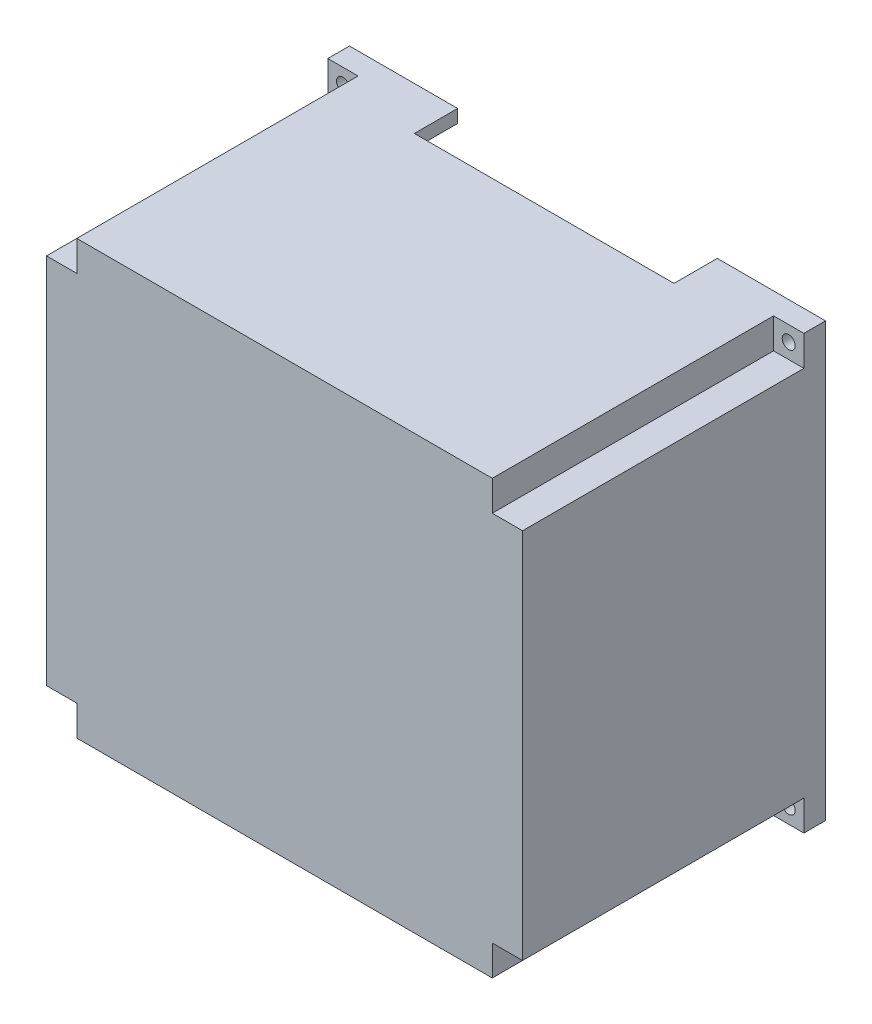
SolidWorks part; units mm, degrees
ref_plane "Front Plane" through (0, 0, 0) normal (0, 0, 1) x (1, 0, 0)
ref_plane "Top Plane" through (0, 0, 0) normal (0, 1, 0) x (1, 0, 0)
ref_plane "Right Plane" through (0, 0, 0) normal (1, 0, 0) x (0, 0, -1)
sketch "Sketch1" plane through (0, 0, 0) normal (0, 1, 0) x (1, 0, 0)
  line L1 (0, 0) -> (2794, 0)
  line L2 (0, 0) -> (0, 1778)
  line L3 (0, 1778) -> (2794, 1778)
  line L4 (2794, 0) -> (2794, 1778)
  dimension "D1" = 1778
  dimension "D2" = 2794
extrude "Boss-Extrude1" add sketch "Sketch1" along normal blind 2540
sketch "Sketch2" plane through (0, 0, -1778) normal (0, 0, -1) x (-1, 0, 0)
  line L0 (-2794, 2540) -> (0, 2540) construction
  line L1 (-2717.8, 2463.8) -> (-76.2, 2463.8)
  line L2 (-2717.8, 2463.8) -> (-2717.8, 76.2)
  line L3 (-2717.8, 76.2) -> (-76.2, 76.2)
  line L4 (-76.2, 2463.8) -> (-76.2, 76.2)
  line L5 (-2717.8, 2463.8) -> (-76.2, 76.2) construction
  line L6 (-2717.8, 76.2) -> (-76.2, 2463.8) construction
  line L7 (-2794, 2540) -> (-2794, 0) construction
  line L8 (-2794, 0) -> (0, 0) construction
  line L9 (0, 2540) -> (0, 0) construction
  point P0 (-1397, 1270)
  dimension "D1" = 76.2
  dimension "D2" = 76.2
  dimension "D3" = 76.2
  dimension "D4" = 76.2
extrude "Cut-Extrude1" cut sketch "Sketch2" against normal blind 1701.8
sketch "Sketch3" plane through (0, 0, -76.2) normal (0, 0, -1) x (-1, 0, 0)
  line L1 (-2717.8, 2463.8) -> (-2540, 2463.8)
  line L2 (-2717.8, 2463.8) -> (-2717.8, 2286)
  line L3 (-2717.8, 2286) -> (-2540, 2286)
  line L4 (-2540, 2463.8) -> (-2540, 2286)
  line L5 (-76.2, 2463.8) -> (-254, 2463.8)
  line L6 (-76.2, 2463.8) -> (-76.2, 2286)
  line L7 (-76.2, 2286) -> (-254, 2286)
  line L8 (-254, 2463.8) -> (-254, 2286)
  line L9 (-2717.8, 76.2) -> (-2540, 76.2)
  line L10 (-2717.8, 76.2) -> (-2717.8, 254)
  line L11 (-2717.8, 254) -> (-2540, 254)
  line L12 (-2540, 76.2) -> (-2540, 254)
  line L13 (-76.2, 76.2) -> (-254, 76.2)
  line L14 (-76.2, 76.2) -> (-76.2, 254)
  line L15 (-76.2, 254) -> (-254, 254)
  line L16 (-254, 76.2) -> (-254, 254)
  dimension "D1" = 177.8
  dimension "D2" = 177.8
  dimension "D3" = 177.8
  dimension "D4" = 177.8
  dimension "D5" = 177.8
  dimension "D6" = 177.8
  dimension "D7" = 177.8
  dimension "D8" = 177.8
extrude "Boss-Extrude2" add sketch "Sketch3" along normal blind 1701.8
sketch "Sketch4" plane through (0, 0, 0) normal (0, 0, 1) x (1, 0, 0)
  line L1 (0, 2540) -> (177.8, 2540)
  line L2 (0, 2540) -> (0, 2362.2)
  line L3 (0, 2362.2) -> (177.8, 2362.2)
  line L4 (177.8, 2540) -> (177.8, 2362.2)
  line L5 (2794, 2540) -> (2616.2, 2540)
  line L6 (2794, 2540) -> (2794, 2362.2)
  line L7 (2794, 2362.2) -> (2616.2, 2362.2)
  line L8 (2616.2, 2540) -> (2616.2, 2362.2)
  line L9 (0, 0) -> (177.8, 0)
  line L10 (0, 0) -> (0, 177.8)
  line L11 (0, 177.8) -> (177.8, 177.8)
  line L12 (177.8, 0) -> (177.8, 177.8)
  line L13 (2794, 0) -> (2616.2, 0)
  line L14 (2794, 0) -> (2794, 177.8)
  line L15 (2794, 177.8) -> (2616.2, 177.8)
  line L16 (2616.2, 0) -> (2616.2, 177.8)
  dimension "D1" = 177.8
  dimension "D2" = 177.8
  dimension "D3" = 177.8
  dimension "D4" = 177.8
  dimension "D5" = 177.8
  dimension "D6" = 177.8
  dimension "D7" = 177.8
  dimension "D8" = 177.8
extrude "Cut-Extrude2" cut sketch "Sketch4" against normal blind 1651
sketch "Sketch5" plane through (0, 0, -1778) normal (0, 0, -1) x (-1, 0, 0)
  line L0 (-2540, 2286) -> (-2540, 2463.8) construction
  line L2 (-2794, 2540) -> (0, 2540) construction
  line L3 (-2540, 76.2) -> (-2540, 254) construction
  line L4 (-2794, 0) -> (0, 0) construction
  line L5 (-254, 254) -> (-254, 76.2) construction
  line L6 (-254, 2463.8) -> (-254, 2286) construction
  circle A0 centre (-2705.1, 2451.1) radius 38.1
  circle A1 centre (-2705.1, 88.9) radius 38.1
  circle A2 centre (-88.9, 2451.1) radius 38.1
  circle A3 centre (-88.9, 88.9) radius 38.1
  point P4 (-2709.2814, 135.0091)
  point P7 (-137.74, 2451.3847)
  point P10 (-137.74, 135.0091)
  point P15 (-2689.3984, 2286)
  dimension "D9" = 76.2
  dimension "D10" = 76.2
  dimension "D11" = 76.2
  dimension "D12" = 76.2
  dimension "D1" = 165.1
  dimension "D2" = 88.9
  dimension "3.5" = 165.1
  dimension "D4" = 88.9
  dimension "D5" = 88.9
  dimension "D6" = 165.1
  dimension "D7" = 88.9
  dimension "D8" = 165.1
extrude "Cut-Extrude5" cut sketch "Sketch5" against normal blind 1651
sketch "Sketch6" plane through (0, 2540, 0) normal (0, 1, 0) x (1, 0, 0)
  line L0 (2794, 1778) -> (0, 1778) construction
  line L1 (635, 1778) -> (2159, 1778)
  line L2 (635, 1778) -> (635, 1524)
  line L3 (635, 1524) -> (2159, 1524)
  line L4 (2159, 1778) -> (2159, 1524)
  line L5 (2794, 1651) -> (2794, 1778) construction
  line L6 (0, 1778) -> (0, 1651) construction
  dimension "D1" = 635
  dimension "D2" = 635
  dimension "D3" = 254
extrude "Cut-Extrude6" cut sketch "Sketch6" against normal blind 254
